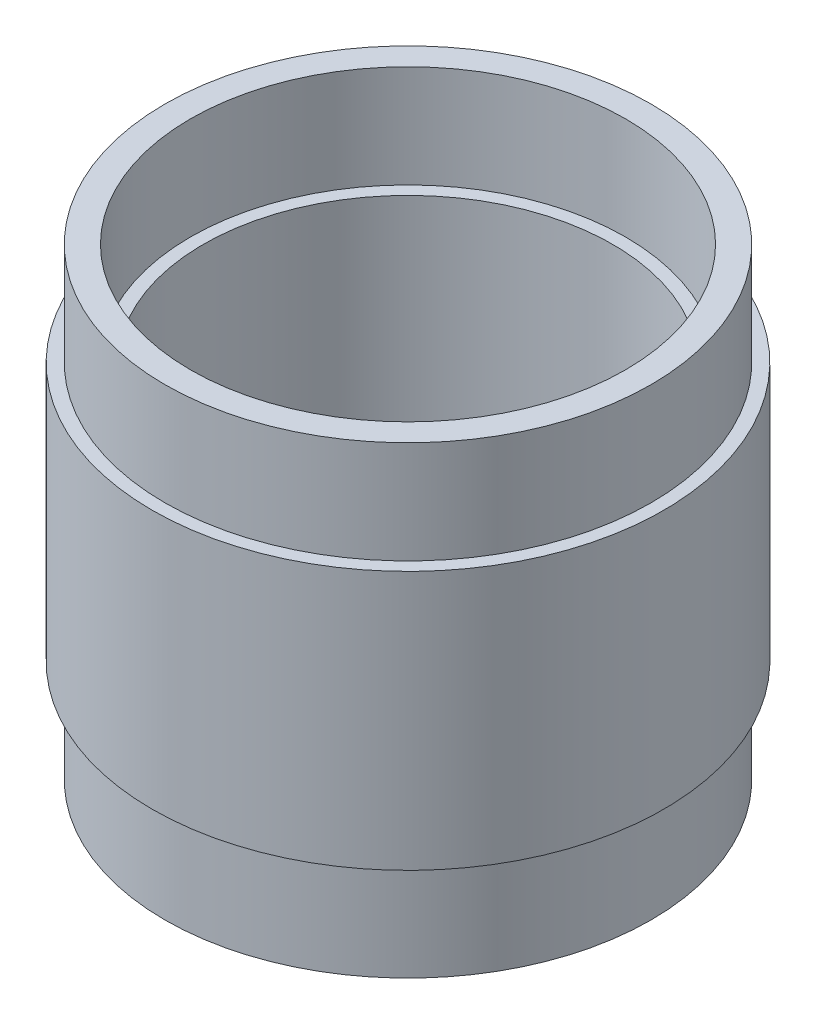
SolidWorks part; units mm, degrees
material "PTFE (general)"
ref_plane "Front Plane" through (0, 0, 0) normal (0, 0, 1) x (1, 0, 0)
ref_plane "Top Plane" through (0, 0, 0) normal (0, 1, 0) x (1, 0, 0)
ref_plane "Right Plane" through (0, 0, 0) normal (1, 0, 0) x (0, 0, -1)
ref_axis "Axis1" through (0, 132.2543, 0) along (0, -1, 0)
sketch "Sketch1" plane through (0, 0, 0) normal (0, 0, 1) x (1, 0, 0)
  line L0 (-60.325, 0) -> (-53.975, 0)
  line L1 (-60.325, 115.062) -> (-53.975, 115.062)
  line L3 (-57.15, 133.8089) -> (-57.15, -35.2387) construction
  line L4 (-53.975, 25.4) -> (-53.975, 0)
  line L5 (-50.8, 25.4) -> (-53.975, 25.4)
  line L6 (-50.8, 89.662) -> (-50.8, 25.4)
  line L7 (-60.325, 115.062) -> (-60.325, 89.662)
  line L8 (-60.325, 89.662) -> (-63.5, 89.662)
  line L9 (-63.5, 89.662) -> (-63.5, 25.4)
  line L10 (-63.5, 25.4) -> (-60.325, 25.4)
  line L11 (-60.325, 25.4) -> (-60.325, 0)
  line L12 (-53.975, 89.662) -> (-50.8, 89.662)
  line L13 (-53.975, 115.062) -> (-53.975, 89.662)
  line L14 (0, 132.2543) -> (0, -55) construction
  point P3 (-57.15, 0)
  point P17 (-57.15, 115.062)
  dimension "D1" = 3.175
  dimension "D2" = 64.262
  dimension "D3" = 25.4
  dimension "D4" = 25.4
  dimension "D5" = 3.175
  dimension "D6" = 57.15
  dimension "D7" = 3.175
revolve "Revolve1" add sketch "Sketch1" angle 360 about axis through (0, 132.2543, 0) along (0, -1, 0)
